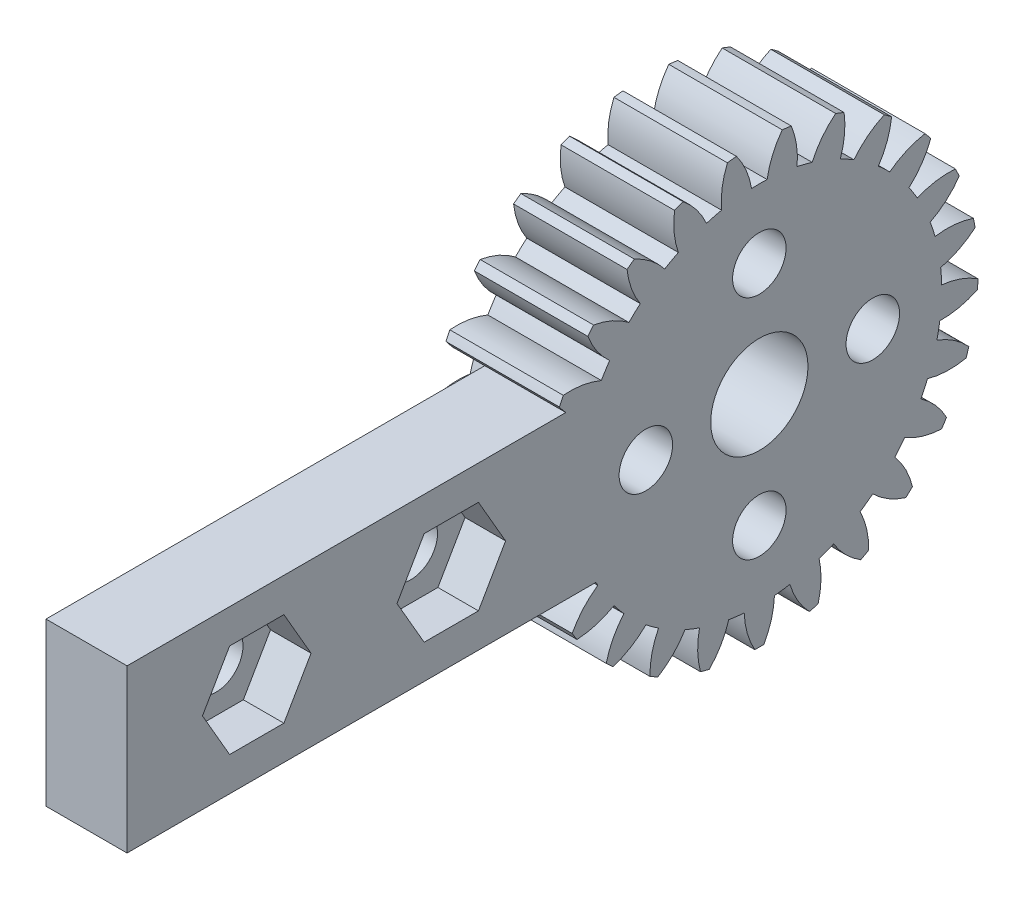
SolidWorks part; units mm, degrees
ref_plane "Plane1" through (0, 0, 0) normal (0, 0, 1) x (1, 0, 0)
ref_plane "Plane2" through (0, 0, 0) normal (0, 1, 0) x (1, 0, 0)
ref_plane "Plane3" through (0, 0, 0) normal (1, 0, 0) x (0, 0, -1)
sketch "HoldingSke" plane through (0, 0, 0) normal (0, 1, 0) x (1, 0, 0)
  line L0 (0, 0) -> (0.9063, -0.4226)
  line L1 (-15, 0) -> (100, 0) construction
  line L2 (0, 0) -> (-2.1039, 2.3779)
  line L3 (0, 0) -> (-11.863, 4.5341)
  line L4 (0, 0) -> (7.8269, 3.6497)
  line L5 (0, 0) -> (-46.8476, -17.4728)
  line L6 (0, 0) -> (-5.8027, -3.9151)
  line L7 (-2.1039, 2.3779) -> (8.6586, 51.2059)
  line L8 (-76.2, 54.61) -> (-76.1, 54.61)
  line L9 (-71.009, 38.7566) -> (-53.1078, 45.2721)
  line L10 (-76.2, 71.12) -> (104.1128, 71.12)
  line L11 (0, 0) -> (-7, 0)
  line L12 (-76.2, 101.6) -> (-76.162, 101.6)
  line L13 (24.9733, 27.94) -> (52.9518, 28.4284)
  line L14 (24.9733, 27.94) -> (24.9743, 27.94)
  line L15 (24.9733, 27.94) -> (100.4006, 29.5858)
  line L16 (-63.627, -1) -> (-12.827, -1)
  circle A0 centre (0, 0) radius 0.4
  circle A1 centre (0, 0) radius 11.249
  circle A2 centre (0, 0) radius 37.5
  circle A3 centre (0, 0) radius 0.4
  dimension "MHD" = 22.498
  dimension "Hub_dia" = 75
  dimension "Bore" = 0.8
  dimension "MBD" = 0.8
  dimension "Num_teeth" = 25
  dimension "Pitch" = 1
  dimension "Overall_len" = 50
  dimension "Show_teeth" = 25
  dimension "Thickness" = 7
  dimension "OAL" = 50.0001
  dimension "T_dim" = 0.1
  dimension "Ap" = 20
  dimension "H" = 19.05
  dimension "Pitch_radius" = 180.3128
  dimension "Width" = 7
  dimension "Backlash" = 0.038
  dimension "Addendum_fac" = 1
  dimension "Dedendum_fac" = 1.25
  dimension "Clearance_fac" = 0.25
  dimension "Dedendum_add" = 0.001
  dimension "Module" = 1
sketch "BasProSke" plane through (0, 0, 0) normal (0, 1, 0) x (1, 0, 0)
  line L0 (-10, 0) -> (60, 0) construction
  line L1 (0, 0) -> (0, 13.5)
  line L2 (0, 0) -> (7, 0)
  line L3 (7, 0) -> (7, 13.5)
  line L4 (7, 13.5) -> (0, 13.5)
  dimension "Thickness" = 7
  dimension "Diameter" = 27
revolve "Base-Revolve" add sketch "BasProSke" angle 360 about L0
sketch "TooCutSke" plane through (0, 0, 0) normal (1, 0, 0) x (0, 0, -1)
  line L1 (0, 0) -> (0, 107) construction
  line L2 (0, 0) -> (-0.8514, 12.471) construction
  line L3 (0, 0) -> (-3.1282, 24.7619) construction
  line L4 (-0.8514, 12.471) -> (-1.5641, 12.3809) construction
  arc A0 (0.4801, 11.2388) -> (-0.4801, 11.2388) centre (0, 0) ccw
  arc A1 (1.4322, 13.4494) -> (-1.4322, 13.4494) centre (0, 0) ccw
  circle A2 centre (0, 0) radius 12.5 construction
  circle A3 centre (0, 0) radius 11.7462 construction
  arc A4 (-0.4801, 11.2388) -> (-1.4322, 13.4494) centre (-5.4133, 10.4244) ccw
  arc A5 (1.4322, 13.4494) -> (0.4801, 11.2388) centre (5.4133, 10.4244) ccw
  dimension "Root_dia" = 22.498
  dimension "Overcut_dia" = 27.0508
  dimension "Pitch_dia" = 25
  dimension "Base_dia" = 23.4923
  dimension "Flank_rad" = 5
  dimension "Half_ang" = 7.2
  dimension "Half_CT" = 0.7184
extrude "ToothCut" cut sketch "TooCutSke" along normal through all
fillet "Breaks" [suppressed] radius 0.02
fillet "RootFillets" [suppressed] radius 0.251
pattern_circular "TeethCuts" count 25 every 14.4 about axis through (-10, 0, 0) along (1, 0, 0) of "ToothCut", "RootFillets", "Breaks"
sketch "HubNeaOneSke" plane through (0, 0, 0) normal (-1, 0, 0) x (0, 0, 1)
  circle A0 centre (0, 0) radius 11.249
  dimension "Diameter" = 22.498
extrude "HubNearOne" [suppressed] add sketch "HubNeaOneSke" along normal blind 43.0001
sketch "HubNeaBotSke" plane through (0, 0, 0) normal (-1, 0, 0) x (0, 0, 1)
  circle A0 centre (0, 0) radius 11.249
  dimension "Diameter" = 22.498
extrude "HubNearBoth" [suppressed] add sketch "HubNeaBotSke" along normal blind 21.5
ref_plane "FarPln" through (7, 0, 0) normal (1, 0, 0) x (0, 0, -1)
sketch "HubFarSke" plane through (7, 0, 0) normal (1, 0, 0) x (0, 0, -1)
  circle A0 centre (0, 0) radius 11.249
  dimension "Diameter" = 22.498
extrude "HubFar" [suppressed] add sketch "HubFarSke" along normal blind 21.5
sketch "BorSke" plane through (0, 0, 0) normal (1, 0, 0) x (0, 0, -1)
  circle A0 centre (0, 0) radius 0.4
  dimension "Diameter" = 0.8
extrude "Bore" cut sketch "BorSke" along normal mid plane 100.0001
sketch "KeySke" plane through (0, 0, 0) normal (1, 0, 0) x (0, 0, -1)
  line L0 (-0.05, 0) -> (-0.05, 0.5)
  line L1 (-0.05, 0.5) -> (0.05, 0.5)
  line L2 (0.05, 0.5) -> (0.05, 0)
  line L3 (0, 0) -> (0, 34) construction
  line L4 (-0.05, 0) -> (0.05, 0)
  dimension "Offset" = 0.5
  dimension "Width" = 0.1
extrude "Keyway" [suppressed] cut sketch "KeySke" along normal mid plane 100.0001
pattern_circular "Keyway2" [suppressed] count 2 every 90 about axis through (-10, 0, 0) along (1, 0, 0)
sketch "草图1" plane through (7, 0, 0) normal (1, 0, 0) x (0, 0, -1)
  circle A0 centre (0, 0) radius 3
  circle A1 centre (0, 7) radius 1.65
  circle A2 centre (7, 0) radius 1.65
  circle A3 centre (-7, 0) radius 1.65
  circle A4 centre (0, -7) radius 1.65
  dimension "D1" = 6
  dimension "D6" = 3.3
  dimension "D7" = 3.3
  dimension "D8" = 3.3
  dimension "D9" = 3.3
  dimension "D2" = 7
  dimension "D3" = 7
  dimension "D4" = 7
  dimension "D5" = 7
extrude "切除-拉伸1" cut sketch "草图1" against normal blind 10
sketch "草图2" plane through (7, 0, 0) normal (1, 0, 0) x (0, 0, -1)
  line L1 (-9, 5) -> (-39, 5)
  line L2 (-9, 5) -> (-9, -5)
  line L3 (-9, -5) -> (-39, -5)
  line L4 (-39, 5) -> (-39, -5)
  circle A0 centre (0, 0) radius 3 construction
  circle A1 centre (-31, 0) radius 1.65
  circle A2 centre (-19, 0) radius 1.65
  dimension "D7" = 3.3
  dimension "D8" = 3.3
  dimension "D1" = 5
  dimension "D2" = 10
  dimension "D3" = 9
  dimension "D4" = 30
  dimension "D5" = 8
  dimension "D6" = 12
  dimension "D9" = 5
extrude "凸台-拉伸2" add sketch "草图2" against normal blind 5
sketch "草图3" plane through (7, 0, 0) normal (1, 0, 0) x (0, 0, -1)
  line L1 (-15.6514, 0) -> (-17.3257, 2.9)
  line L2 (-17.3257, 2.9) -> (-20.6743, 2.9)
  line L3 (-20.6743, 2.9) -> (-22.3486, 0)
  line L4 (-22.3486, 0) -> (-20.6743, -2.9)
  line L5 (-20.6743, -2.9) -> (-17.3257, -2.9)
  line L6 (-17.3257, -2.9) -> (-15.6514, 0)
  line L7 (-27.6514, 0) -> (-29.3257, 2.9)
  line L8 (-29.3257, 2.9) -> (-32.6743, 2.9)
  line L9 (-32.6743, 2.9) -> (-34.3486, 0)
  line L10 (-34.3486, 0) -> (-32.6743, -2.9)
  line L11 (-32.6743, -2.9) -> (-29.3257, -2.9)
  line L12 (-29.3257, -2.9) -> (-27.6514, 0)
  circle A0 centre (-19, 0) radius 2.9 construction
  circle A1 centre (-31, 0) radius 2.9 construction
  dimension "D1" = 5.8
  dimension "D2" = 5.8
extrude "切除-拉伸2" cut sketch "草图3" against normal blind 2.5
equation "' \"Module@HoldingSke\" = 6.35"
equation "' \"Num_teeth@HoldingSke\" = 12"
equation "' \"Ap@HoldingSke\" =  20"
equation "' \"Ap@HoldingSke\" = 20"
equation "' \"Width@HoldingSke\" = 0.5 * 25.4"
equation "' \"Hub_dia@HoldingSke\"= 1 * 25.4"
equation "' \"Hub_dia@HoldingSke\" = 1 * 25.4"
equation "' \"Overall_len@HoldingSke\" = 1.0 * 25.4"
equation "' \"Bore@HoldingSke\" = 0.75 * 25.4"
equation "' \"T_dim@HoldingSke\" = 0.1 * 25.4"
equation "' \"Width@KeySke\" = 0.25 * 25.4"
equation "' \"Show_teeth@HoldingSke\" = 13"
equation "' \"Backlash@HoldingSke\" = 0.009 * 25.4"
equation "' \"Addendum_fac@HoldingSke\" = 1.0"
equation "' \"Dedendum_fac@HoldingSke\" = 1.25"
equation "' \"Dedendum_add@HoldingSke\" = 0.00005 * 25.4"
equation "' \"Clearance_fac@HoldingSke\" = 0.25"
equation "\"Pitch@HoldingSke\" = 1 / \"Module@HoldingSke\""
equation "\"Overcut_dia@TooCutSke\" = (\"Num_teeth@HoldingSke\" + 2 * \"Addendum_fac@HoldingSke\") / \"Pitch@HoldingSke\" + 0.002 * 25.4"
equation "\"Pitch_dia@TooCutSke\" = \"Num_teeth@HoldingSke\" / \"Pitch@HoldingSke\""
equation "\"Base_dia@TooCutSke\" = \"Num_teeth@HoldingSke\" / \"Pitch@HoldingSke\" * cos((\"Ap@HoldingSke\"  * 3.14159265 / 180))"
equation "\"Root_dia@TooCutSke\" = (\"Num_teeth@HoldingSke\" + 2) / \"Pitch@HoldingSke\" - 2 * (\"Addendum_fac@HoldingSke\" + \"Dedendum_fac@HoldingSke\") / \"Pitch@HoldingSke\" - \"Dedendum_add@HoldingSke\" * 2"
equation "\"Half_ang@TooCutSke\" = 180 / \"Num_teeth@HoldingSke\""
equation "\"Half_CT@TooCutSke\" = \"Num_teeth@HoldingSke\" / \"Pitch@HoldingSke\" * sin((3.14159265 / 2 / \"Num_teeth@HoldingSke\")) / 2 - 7 * \"Backlash@HoldingSke\" / 4"
equation "\"Flank_rad@TooCutSke\" = \"Num_teeth@HoldingSke\" / \"Pitch@HoldingSke\" / 5"
equation "\"Radius@RootFillets\" = \"Clearance_fac@HoldingSke\" / \"Pitch@HoldingSke\" + \"Dedendum_add@HoldingSke\""
equation "\"Break_rad@Breaks\" = 0.02 / \"Pitch@HoldingSke\""
equation "\"Thickness@HoldingSke\" = \"Width@HoldingSke\""
equation "\"OAL@HoldingSke\" = \"Thickness@HoldingSke\""
equation "\"MHD@HoldingSke\" = (\"Num_teeth@HoldingSke\" + 2) / \"Pitch@HoldingSke\" - 2 * (\"Addendum_fac@HoldingSke\" + \"Dedendum_fac@HoldingSke\")  / \"Pitch@HoldingSke\" - \"Dedendum_add@HoldingSke\" * 2"
equation "\"MBD@HoldingSke\" = (\"Num_teeth@HoldingSke\" + 2) / \"Pitch@HoldingSke\" - 2 * (\"Addendum_fac@HoldingSke\" + \"Dedendum_fac@HoldingSke\")  / \"Pitch@HoldingSke\" - \"Dedendum_add@HoldingSke\" * 2 - 0.002 * 25.4"
equation "\"MHD@HoldingSke\" = ((sgn( \"MHD@HoldingSke\" - \"Hub_dia@HoldingSke\" )-1)*( \"MHD@HoldingSke\" - \"Hub_dia@HoldingSke\" ))/-2+ \"Hub_dia@HoldingSke\""
equation "\"MBD@HoldingSke\" = ((sgn( \"MBD@HoldingSke\" - \"Bore@HoldingSke\" )-1)*( \"MBD@HoldingSke\" - \"Bore@HoldingSke\" ))/-2+ \"Bore@HoldingSke\""
equation "\"OAL@HoldingSke\" = ((sgn( \"OAL@HoldingSke\" - \"Overall_len@HoldingSke\" )+1)*( \"OAL@HoldingSke\" - \"Overall_len@HoldingSke\" ))/2 + \"Overall_len@HoldingSke\" + 0.000002 * 25.4"
equation "\"Num_teeth@TeethCuts\" = int( \"Show_teeth@HoldingSke\" ) + 1"
equation "\"Num_teeth@TeethCuts\" = ((sgn( \"Num_teeth@TeethCuts\" - \"Num_teeth@HoldingSke\" )-1)*( \"Num_teeth@TeethCuts\" - \"Num_teeth@HoldingSke\" ))/-2+ \"Num_teeth@HoldingSke\""
equation "\"Num_teeth@TeethCuts\" = ((sgn( \"Num_teeth@TeethCuts\" - 2.0)+1)*( \"Num_teeth@TeethCuts\" - 2.0))/2 +2.0"
equation "\"Angle@TeethCuts\" = 360.0 / \"Num_teeth@HoldingSke\""
equation "\"Diameter@BasProSke\" = (\"Num_teeth@HoldingSke\" + 2 * \"Addendum_fac@HoldingSke\") / \"Pitch@HoldingSke\""
equation "\"Thickness@BasProSke\"  = \"Thickness@HoldingSke\""
equation "' \"Fillet_rad@BasProSke\" =  \"Thickness@HoldingSke\" * 0.05"
equation "' \"Fillet_rad@BasProSke\" = \"Thickness@HoldingSke\" * 0.05"
equation "\"MHD@HoldingSke\" = ((sgn( \"MHD@HoldingSke\" - \"Root_dia@TooCutSke\" )-1)*( \"MHD@HoldingSke\" - \"Root_dia@TooCutSke\" ))/-2+ \"Root_dia@TooCutSke\""
equation "\"Diameter@HubNeaOneSke\" = \"MHD@HoldingSke\""
equation "\"Length@HubNearOne\" = \"OAL@HoldingSke\" - \"Thickness@BasProSke\""
equation "\"Diameter@HubNeaBotSke\" = \"MHD@HoldingSke\""
equation "\"Length@HubNearBoth\" = ( \"OAL@HoldingSke\" - \"Thickness@BasProSke\" ) / 2.0"
equation "\"Thickness@FarPln\" = \"Thickness@BasProSke\""
equation "\"Diameter@HubFarSke\" = \"MHD@HoldingSke\""
equation "\"Length@HubFar\" = ( \"OAL@HoldingSke\" - \"Thickness@BasProSke\" ) / 2.0"
equation "\"Diameter@BorSke\" = \"MBD@HoldingSke\""
equation "\"D1@Bore\" = \"OAL@HoldingSke\" * 2.0"
equation "\"D1@Keyway\" = \"OAL@HoldingSke\" * 2.0"
equation "\"Offset@KeySke\" = \"T_dim@HoldingSke\" + \"MBD@HoldingSke\" / 2.0"
